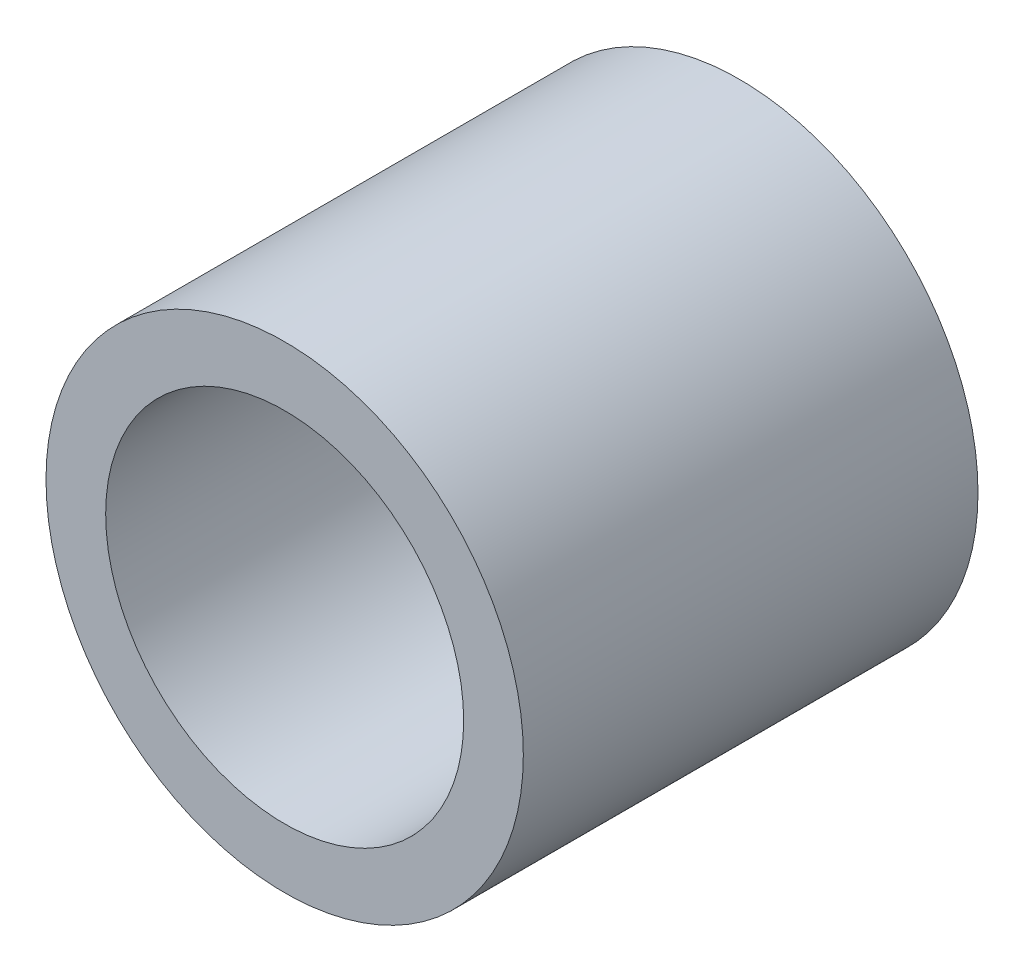
SolidWorks part; units mm, degrees
ref_plane "Front Plane" through (0, 0, 0) normal (0, 0, 1) x (1, 0, 0)
ref_plane "Top Plane" through (0, 0, 0) normal (0, 1, 0) x (1, 0, 0)
ref_plane "Right Plane" through (0, 0, 0) normal (1, 0, 0) x (0, 0, -1)
sketch "Sketch1" plane through (0, 0, 0) normal (0, 0, 1) x (1, 0, 0)
  circle A0 centre (0, 0) radius 1.5
  circle A1 centre (0, 0) radius 2
extrude "Extrude1" add sketch "Sketch1" along normal blind 3.81
